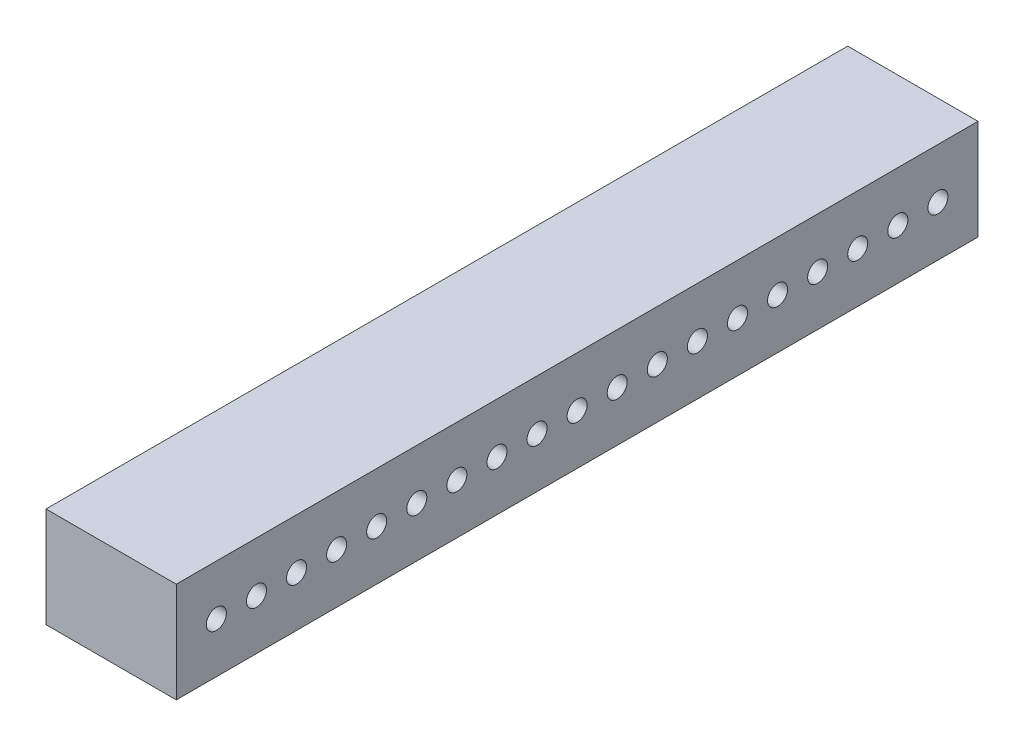
SolidWorks part; units mm, degrees
ref_plane "Front Plane" through (0, 0, 0) normal (0, 0, 1) x (1, 0, 0)
ref_plane "Top Plane" through (0, 0, 0) normal (0, 1, 0) x (1, 0, 0)
ref_plane "Right Plane" through (0, 0, 0) normal (1, 0, 0) x (0, 0, -1)
sketch "Sketch1" plane through (0, 0, 0) normal (1, 0, 0) x (0, 0, -1)
  line L1 (-200, 25) -> (200, 25)
  line L2 (-200, 25) -> (-200, -25)
  line L3 (-200, -25) -> (200, -25)
  line L4 (200, 25) -> (200, -25)
  line L5 (-200, 25) -> (200, -25) construction
  line L6 (-200, -25) -> (200, 25) construction
  point P0 (0, 0)
  dimension "D1" = 400
  dimension "D2" = 50
extrude "Boss-Extrude1" add sketch "Sketch1" along normal blind 65
sketch "Sketch2" plane through (65, 0, 0) normal (1, 0, 0) x (0, 0, -1)
  line L0 (200, 25) -> (-200, 25) construction
  line L1 (-200, 25) -> (-200, -25) construction
  circle A0 centre (-180, 0) radius 5
  circle A1 centre (-160, 0) radius 5
  circle A2 centre (-140, 0) radius 5
  circle A3 centre (-120, 0) radius 5
  circle A4 centre (-100, 0) radius 5
  circle A5 centre (-80, 0) radius 5
  circle A6 centre (-60, 0) radius 5
  circle A7 centre (-40, 0) radius 5
  circle A8 centre (-20, 0) radius 5
  circle A9 centre (0, 0) radius 5
  circle A10 centre (20, 0) radius 5
  circle A11 centre (40, 0) radius 5
  circle A12 centre (60, 0) radius 5
  circle A13 centre (80, 0) radius 5
  circle A14 centre (100, 0) radius 5
  circle A15 centre (120, 0) radius 5
  circle A16 centre (140, 0) radius 5
  circle A17 centre (160, 0) radius 5
  circle A18 centre (180, 0) radius 5
  dimension "D1" = 10
  dimension "D2" = 25
  dimension "D3" = 20
  dimension "D4" = 19
extrude "Cut-Extrude1" cut sketch "Sketch2" against normal through all
